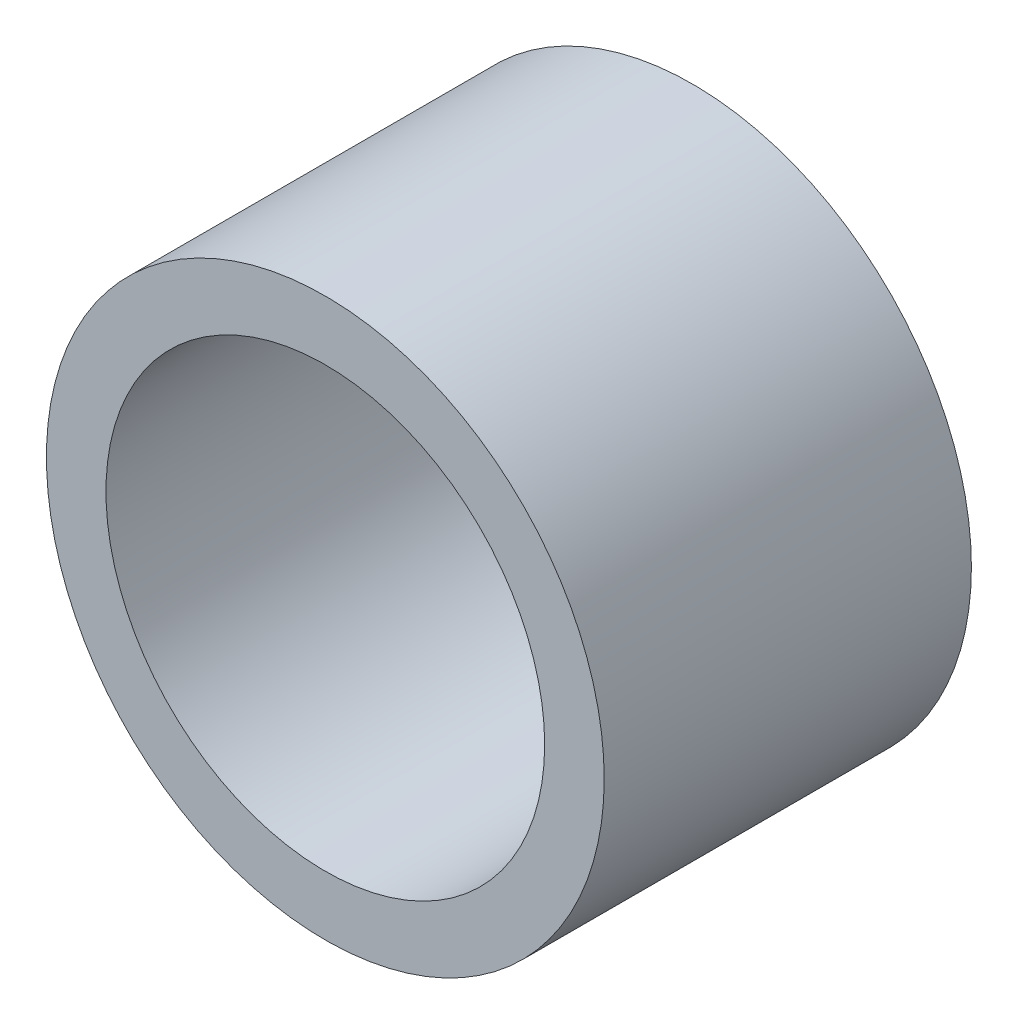
SolidWorks part; units mm, degrees
ref_plane "Front Plane" through (0, 0, 0) normal (0, 0, 1) x (1, 0, 0)
ref_plane "Top Plane" through (0, 0, 0) normal (0, 1, 0) x (1, 0, 0)
ref_plane "Right Plane" through (0, 0, 0) normal (1, 0, 0) x (0, 0, -1)
sketch "Sketch1" plane through (0, 0, 0) normal (0, 0, 1) x (1, 0, 0)
  circle A0 centre (0, 6.1229) radius 38.5844
  circle A1 centre (0, 6.1229) radius 30.3472
extrude "Boss-Extrude1" add sketch "Sketch1" along normal blind 50.8
